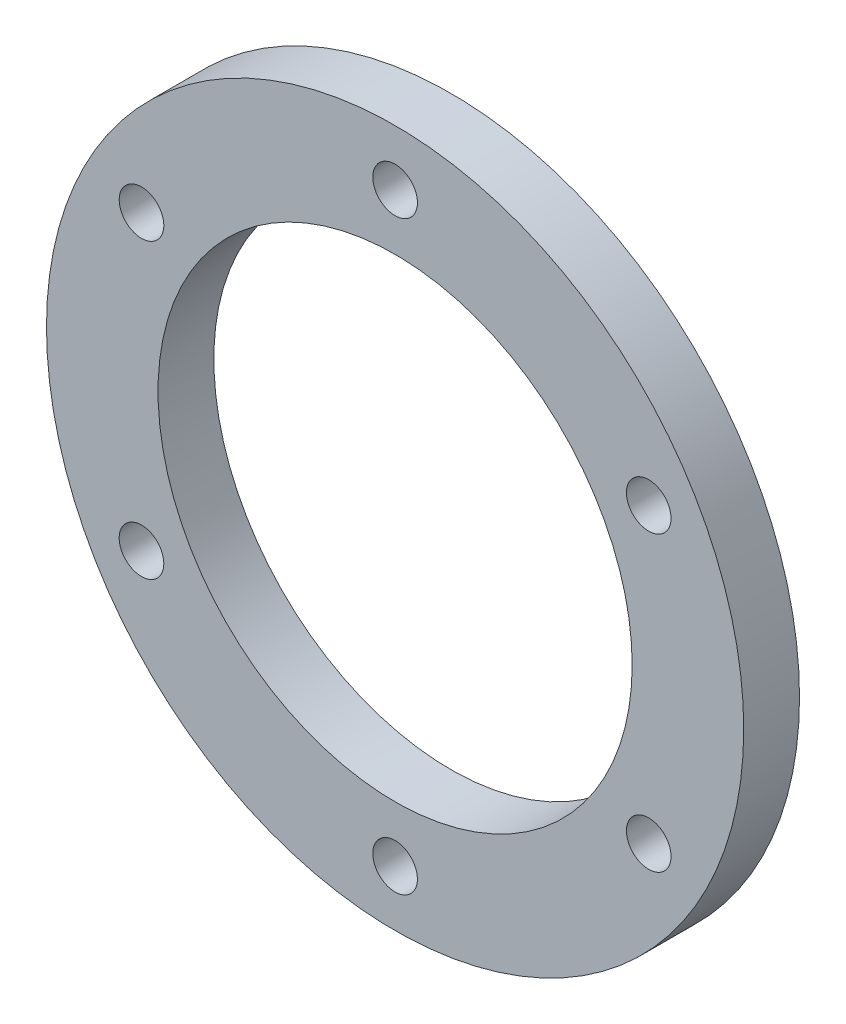
SolidWorks part; units mm, degrees
material "Brass"
ref_plane "Front Plane" through (0, 0, 0) normal (0, 0, 1) x (1, 0, 0)
ref_plane "Top Plane" through (0, 0, 0) normal (0, 1, 0) x (1, 0, 0)
ref_plane "Right Plane" through (0, 0, 0) normal (1, 0, 0) x (0, 0, -1)
sketch "Sketch1" plane through (0, 0, 0) normal (0, 0, 1) x (1, 0, 0)
  circle A0 centre (0, 0) radius 42.5
  circle A1 centre (0, 0) radius 62.5
  dimension "D1" = 85
  dimension "D2" = 125
extrude "Body" add sketch "Sketch1" along normal mid plane 10
sketch "Sketch2" plane through (0, 0, 5) normal (0, 0, 1) x (1, 0, 0)
  line L0 (0, -71.4075) -> (0, 70.4111) construction
  circle A0 centre (0, 52.5) radius 4
  circle A1 centre (0, 0) radius 52.5 construction
  dimension "D1" = 8
  dimension "D2" = 105
extrude "Cut-Extrude1" cut sketch "Sketch2" against normal through all
pattern_circular "Holes" count 6 over 360 about axis through (0, 0, 0) along (0, 0, 1) of "Cut-Extrude1"
